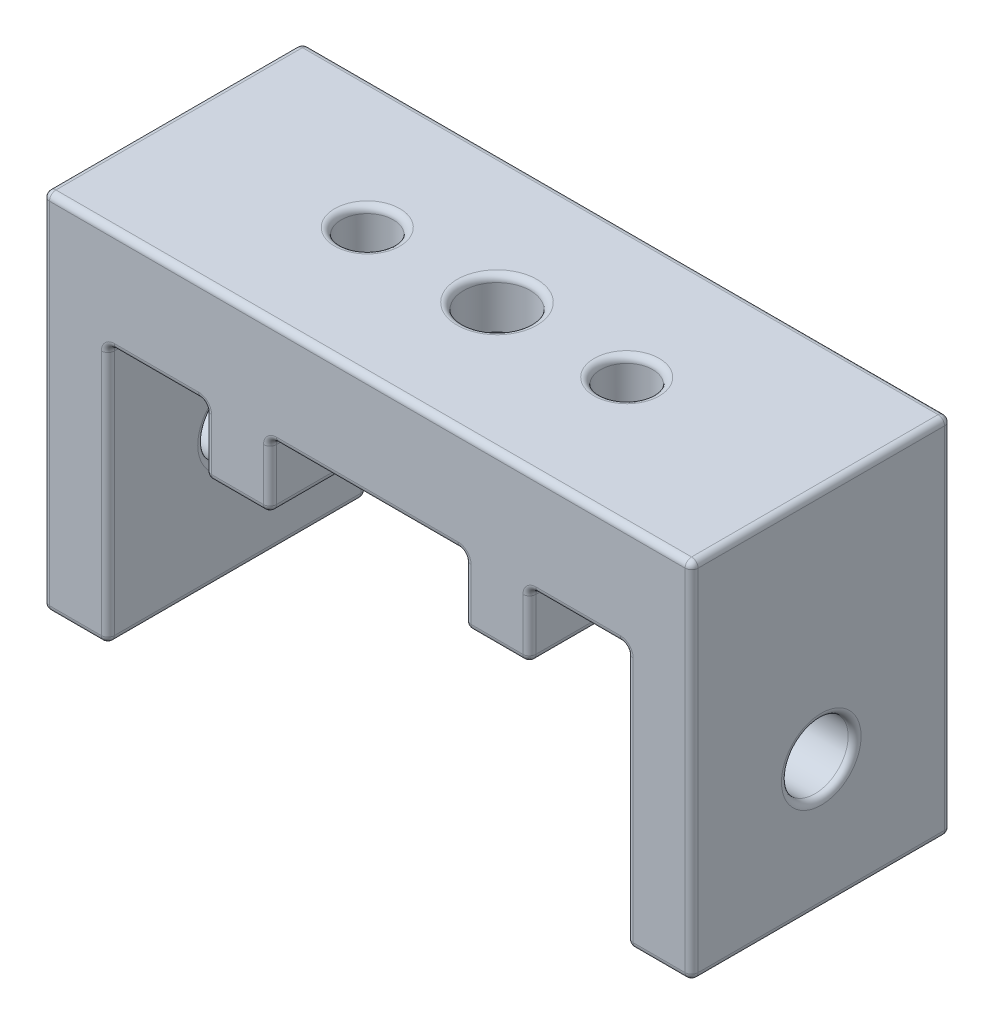
SolidWorks part; units mm, degrees
ref_plane "Front Plane" through (0, 0, 0) normal (0, 0, 1) x (1, 0, 0)
ref_plane "Top Plane" through (0, 0, 0) normal (0, 1, 0) x (1, 0, 0)
ref_plane "Right Plane" through (0, 0, 0) normal (1, 0, 0) x (0, 0, -1)
sketch "Sketch1" plane through (0, 0, 0) normal (0, 0, 1) x (1, 0, 0)
  line L0 (0, 0) -> (6.35, 0) construction
  line L1 (0, 0) -> (6.35, 0)
  line L2 (0, 0) -> (0, 35.56)
  line L3 (0, 35.56) -> (63.5, 35.56)
  line L4 (63.5, 0) -> (63.5, 35.56)
  line L5 (6.35, 0) -> (6.35, 25.4) construction
  line L6 (6.35, 25.4) -> (57.15, 25.4) construction
  line L7 (57.15, 25.4) -> (57.15, 0) construction
  line L8 (57.15, 0) -> (63.5, 0) construction
  line L9 (6.35, 0) -> (6.35, 25.4)
  line L10 (6.35, 25.4) -> (57.15, 25.4)
  line L11 (57.15, 25.4) -> (57.15, 0)
  line L12 (57.15, 0) -> (63.5, 0)
  dimension "D1" = 6.35
  dimension "D2" = 6.35
  dimension "D3" = 50.8
  dimension "D4" = 63.5
  dimension "D5" = 35.56
  dimension "D6" = 25.4
extrude "Boss-Extrude1" add sketch "Sketch1" along normal blind 25.4
sketch "Sketch2" plane through (0, 25.4, 0) normal (0, -1, 0) x (1, 0, 0)
  line L0 (0, 0) -> (19.05, 0) construction
  line L2 (19.05, 0) -> (19.05, 3.81) construction
  line L4 (22.225, 7.62) -> (15.875, 7.62)
  line L5 (22.225, 7.62) -> (22.225, 0)
  line L6 (22.225, 0) -> (15.875, 0)
  line L7 (15.875, 7.62) -> (15.875, 0)
  line L8 (22.225, 7.62) -> (15.875, 0) construction
  line L9 (22.225, 0) -> (15.875, 7.62) construction
  dimension "D1" = 6.35
  dimension "D2" = 7.62
  dimension "D3" = 12.7
extrude "Boss-Extrude2" add sketch "Sketch2" along normal blind 6.35
ref_plane "Plane1" through (0, 0, 12.7) normal (0, 0, 1) x (1, 0, 0)
mirror "Mirror1" about plane through (0, 0, 12.7) normal (0, 0, 1) of "Boss-Extrude2"
hole_wizard "1/4-20 Tapped Hole1" positions "Sketch4" profile "Sketch3" tap size "1/4-20" standard "Ansi Inch" end condition through all
sketch "Sketch4" plane through (0, 35.56, 0) normal (0, 1, 0) x (-1, 0, 0)
  line L0 (-63.5, 0) -> (0, 0) construction
  line L1 (0, 25.4) -> (0, 0) construction
  point P0 (-19.05, 12.7)
  point P2 (-31.75, 0)
  dimension "D1" = 12.7
  dimension "D2" = 19.05
sketch "Sketch3" plane through (19.05, 35.56, 12.7) normal (1, 0, 0) x (0, 0, 1)
  line L0 (0, 0) -> (0, 35.56)
  line L1 (0, 35.56) -> (2.5527, 35.56)
  line L2 (2.5527, 35.56) -> (2.5527, 0)
  line L5 (2.5527, 0) -> (0, 0)
  line L11 (0, -6.35) -> (0, 107.95) construction
  dimension "Thru Tap Drill Dia." = 5.1054
  dimension "Thru Tap Drill Depth" = 35.56
cosmetic thread "Hole Thread1" parameters "D2"=6.35
hole_wizard "#97 (0.0059) Diameter Hole1" positions "Sketch6" profile "Sketch5" hole size "#97" standard "Ansi Inch"
sketch "Sketch6" plane through (6.35, 0, 0) normal (1, 0, 0) x (0, 0, -1)
  line L0 (0, 0) -> (0, 25.4) construction
  line L1 (-25.4, 25.4) -> (0, 25.4) construction
  point P0 (-12.7, 12.7)
  dimension "D1" = 12.7
  dimension "D2" = 12.7
sketch "Sketch5" plane through (6.35, 12.7, 12.7) normal (0, 1, 0) x (0, 0, -1)
  line L0 (0, 0) -> (0, 6.35)
  line L1 (0, 6.35) -> (3.2639, 6.35)
  line L2 (3.2639, 6.35) -> (3.2639, 0)
  line L5 (3.2639, 0) -> (0, 0)
  line L11 (0, -6.35) -> (0, 107.95) construction
  dimension "Thru Hole Dia." = 6.5278
  dimension "Thru Hole Depth" = 6.35
hole_wizard "#97 (0.0059) Diameter Hole2" positions "Sketch8" profile "Sketch7" hole size "#97" standard "Ansi Inch" end condition through all
sketch "Sketch8" plane through (57.15, 0, 0) normal (-1, 0, 0) x (0, 0, 1)
  line L0 (25.4, 25.4) -> (0, 25.4) construction
  line L1 (0, 25.4) -> (0, 0) construction
  point P0 (12.7, 12.7)
  dimension "D1" = 12.7
  dimension "D2" = 12.7
sketch "Sketch7" plane through (57.15, 12.7, 12.7) normal (0, 1, 0) x (0, 0, 1)
  line L0 (0, 0) -> (0, 6.35)
  line L1 (0, 6.35) -> (3.2639, 6.35)
  line L2 (3.2639, 6.35) -> (3.2639, 0)
  line L5 (3.2639, 0) -> (0, 0)
  line L11 (0, -6.35) -> (0, 107.95) construction
  dimension "Thru Hole Dia." = 6.5278
  dimension "Thru Hole Depth" = 6.35
ref_plane "Plane2" through (31.75, 0, 0) normal (1, 0, 0) x (0, 0, -1)
mirror "Mirror2" about plane through (31.75, 0, 0) normal (1, 0, 0) of "1/4-20 Tapped Hole1"
mirror "Mirror3" about plane through (31.75, 0, 0) normal (1, 0, 0) of "Boss-Extrude2", "Mirror1"
hole_wizard "#97 (0.0059) Diameter Hole3" positions "Sketch12" profile "Sketch11" hole size "#97" standard "Ansi Inch" end condition through all
sketch "Sketch12" plane through (0, 25.4, 0) normal (0, -1, 0) x (1, 0, 0)
  line L0 (22.225, 0) -> (41.275, 0) construction
  line L1 (6.35, 25.4) -> (6.35, 0) construction
  point P0 (31.75, 12.7)
  dimension "D1" = 12.7
  dimension "D2" = 25.4
sketch "Sketch11" plane through (31.75, 25.4, 12.7) normal (1, 0, 0) x (0, 0, -1)
  line L0 (0, 0) -> (0, 10.16)
  line L1 (0, 10.16) -> (3.2639, 10.16)
  line L2 (3.2639, 10.16) -> (3.2639, 0)
  line L5 (3.2639, 0) -> (0, 0)
  line L11 (0, -6.35) -> (0, 107.95) construction
  dimension "Thru Hole Dia." = 6.5278
  dimension "Thru Hole Depth" = 10.16
fillet "Fillet2" radius 0.635 81 edges at (47.625, 25.4, 21.59) (19.05, 25.4, 17.78) (15.875, 25.4, 3.81) (44.45, 25.4, 17.78) (47.625, 22.225, 7.62) (41.275, 22.225, 7.62) (44.45, 25.4, 7.62) (41.275, 19.05, 3.81) (44.45, 19.05, 7.62) (47.625, 19.05, 3.81) (15.875, 19.05, 21.59) (15.875, 22.225, 17.78) (15.875, 25.4, 21.59) (22.225, 22.225, 17.78) (22.225, 19.05, 21.59) (22.225, 25.4, 21.59) (6.35, 0, 12.7) (6.35, 25.4, 12.7) (6.35, 12.7, 9.4361) (3.175, 0, 0) (3.175, 0, 25.4) (6.35, 12.7, 0) (6.35, 12.7, 25.4) (11.1125, 25.4, 0) (15.875, 22.225, 0) (19.05, 19.05, 0) (22.225, 22.225, 0) (31.75, 25.4, 0) (41.275, 22.225, 0) (44.45, 19.05, 0) (47.625, 22.225, 0) (52.3875, 25.4, 0) (57.15, 12.7, 0) (57.15, 12.7, 25.4) (60.325, 0, 0) (60.325, 0, 25.4) (63.5, 17.78, 0) (63.5, 17.78, 25.4) (31.75, 35.56, 0) (31.75, 35.56, 25.4) (0, 17.78, 0) (0, 17.78, 25.4) (52.3875, 25.4, 25.4) (47.625, 22.225, 25.4) (47.625, 22.225, 17.78) (44.45, 19.05, 25.4) (44.45, 19.05, 17.78) (41.275, 22.225, 17.78) (41.275, 22.225, 25.4) (31.75, 25.4, 25.4) (22.225, 22.225, 25.4) (19.05, 19.05, 17.78) (19.05, 19.05, 25.4) (15.875, 22.225, 25.4) (11.1125, 25.4, 25.4) (15.875, 22.225, 7.62) (15.875, 19.05, 3.81) (19.05, 19.05, 7.62) (22.225, 19.05, 3.81) (22.225, 22.225, 7.62) (19.05, 25.4, 7.62) (22.225, 25.4, 3.81) (47.625, 25.4, 3.81) (41.275, 25.4, 3.81) (47.625, 19.05, 21.59) (41.275, 25.4, 21.59) (41.275, 19.05, 21.59) (57.15, 25.4, 12.7) (57.15, 12.7, 15.9639) (0, 12.7, 9.4361) (63.5, 35.56, 12.7) (0, 35.56, 12.7) (0, 0, 12.7) (57.15, 0, 12.7) (63.5, 0, 12.7) (44.45, 25.4, 15.2527) (44.45, 35.56, 15.2527) (19.05, 35.56, 15.2527) (63.5, 12.7, 15.9639) (31.75, 25.4, 9.4361) (31.75, 35.56, 9.4361)
sketch "Sketch13" plane through (0, 25.4, 0) normal (0, -1, 0) x (1, 0, 0)
  line L0 (6.985, 24.765) -> (56.515, 0.635) construction
  line L2 (31.75, 19.0058) -> (26.289, 15.8529)
  line L3 (26.289, 15.8529) -> (26.289, 9.5471)
  line L4 (26.289, 9.5471) -> (31.75, 6.3942)
  line L5 (31.75, 6.3942) -> (37.211, 9.5471)
  line L6 (37.211, 9.5471) -> (37.211, 15.8529)
  line L7 (37.211, 15.8529) -> (31.75, 19.0058)
  circle A0 centre (31.75, 12.7) radius 5.461 construction
  point P4 (31.75, 12.7)
  dimension "D1" = 10.922
extrude "Boss-Extrude3" add sketch "Sketch13" against normal blind 5.334 separate body
combine bodies "Combine1" operation type subtract main body 109 bodies to subtract 110
